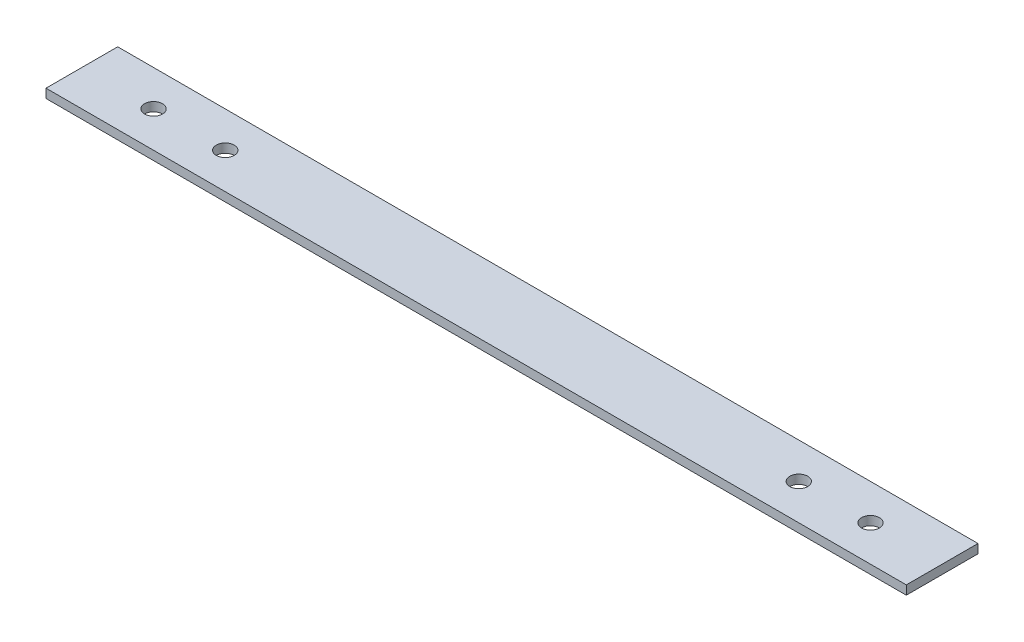
SolidWorks part; units mm, degrees
ref_plane "Front Plane" through (0, 0, 0) normal (0, 0, 1) x (1, 0, 0)
ref_plane "Top Plane" through (0, 0, 0) normal (0, 1, 0) x (1, 0, 0)
ref_plane "Right Plane" through (0, 0, 0) normal (1, 0, 0) x (0, 0, -1)
sketch "Sketch1" plane through (0, 0, 0) normal (0, 1, 0) x (1, 0, 0)
  line L1 (0, 0) -> (609.6, 0)
  line L2 (0, 0) -> (0, 50.8)
  line L3 (0, 50.8) -> (609.6, 50.8)
  line L4 (609.6, 0) -> (609.6, 50.8)
  dimension "D1" = 50.8
  dimension "D2" = 609.6
extrude "Boss-Extrude1" add sketch "Sketch1" along normal blind 6.35
sketch "Sketch2" plane through (0, 6.35, 0) normal (0, 1, 0) x (1, 0, 0)
  line L0 (609.6, 25.4) -> (0, 25.4) construction
  line L1 (609.6, 0) -> (609.6, 50.8) construction
  line L2 (0, 50.8) -> (0, 0) construction
  circle A0 centre (558.8, 25.4) radius 6.35
  circle A1 centre (50.8, 25.4) radius 6.35
  circle A2 centre (101.6, 25.4) radius 6.35
  circle A3 centre (508, 25.4) radius 6.35
  dimension "D1" = 50.8
  dimension "D2" = 50.8
  dimension "D5" = 12.7
  dimension "D6" = 12.7
  dimension "D7" = 12.7
  dimension "D8" = 12.7
  dimension "D3" = 50.8
  dimension "D4" = 101.6
extrude "Cut-Extrude1" cut sketch "Sketch2" against normal through all
